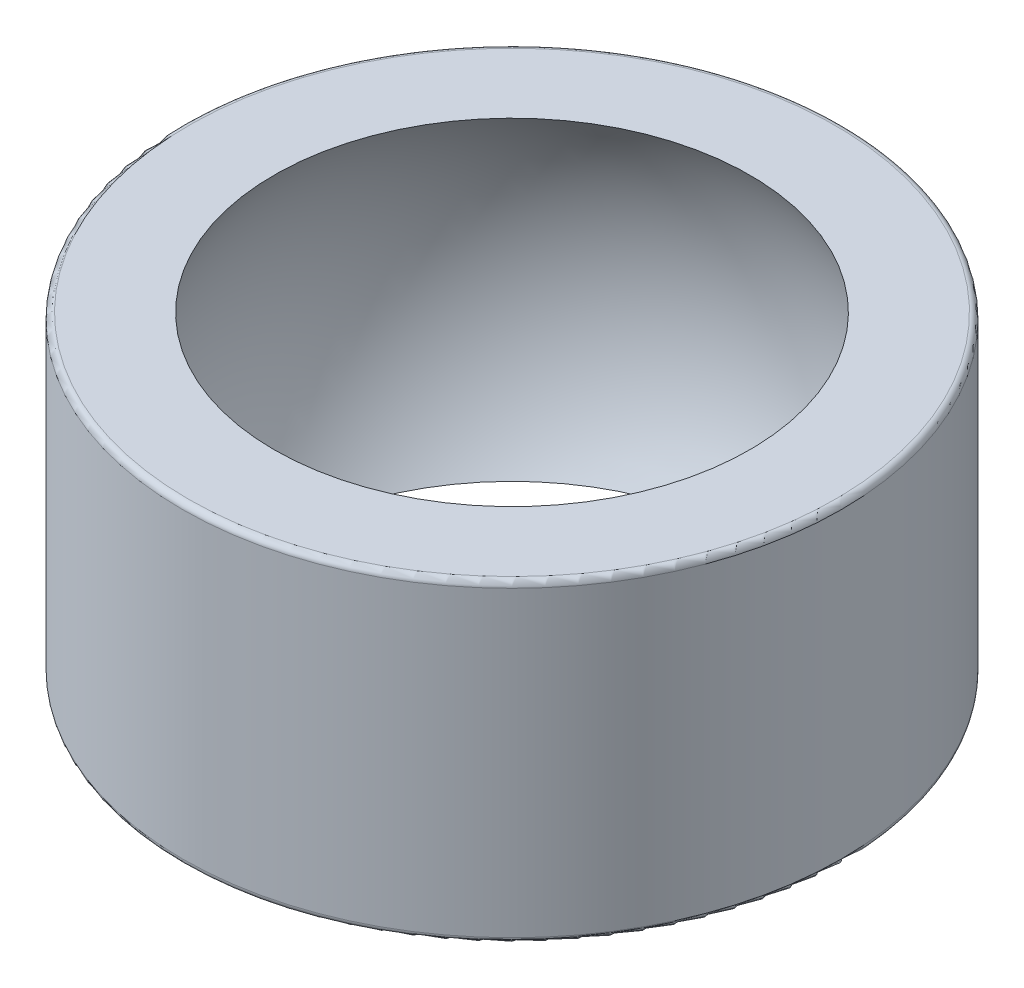
SolidWorks part; units mm, degrees
material "1.0545 (S355N)"
ref_plane "Płaszczyzna przednia" through (0, 0, 0) normal (0, 0, 1) x (1, 0, 0)
ref_plane "Płaszczyzna górna" through (0, 0, 0) normal (0, 1, 0) x (1, 0, 0)
ref_plane "Płaszczyzna prawa" through (0, 0, 0) normal (1, 0, 0) x (0, 0, -1)
sketch "Szkic1" plane through (0, 0, 0) normal (0, 1, 0) x (1, 0, 0)
  circle A0 centre (0, 0) radius 11
  dimension "d2" = 22
extrude "Dodanie-wyciągnięcie1" add sketch "Szkic1" along normal mid plane 10.5
sketch "Szkic3" plane through (0, 0, 0) normal (0, 0, 1) x (1, 0, 0)
  line L0 (0, -9.52) -> (0, 9.52)
  arc A0 (0, -9.52) -> (0, 9.52) centre (0, 0) ccw
  dimension "d3" = 19.04
revolve "Wycięcie-obrót1" cut sketch "Szkic3" angle 360 about L0
fillet "Zaokrąglenie1" radius 0.2 2 edges at (0, 5.25, 11) (0, -5.25, 11)
